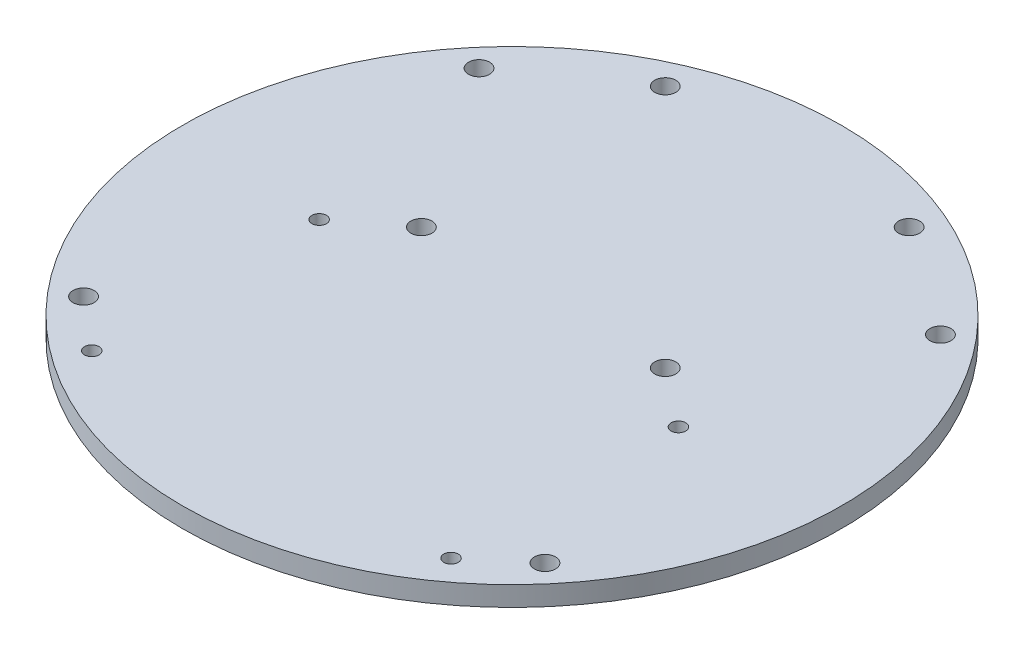
SolidWorks part; units mm, degrees
ref_plane "Front Plane" through (0, 0, 0) normal (0, 0, 1) x (1, 0, 0)
ref_plane "Top Plane" through (0, 0, 0) normal (0, 1, 0) x (1, 0, 0)
ref_plane "Right Plane" through (0, 0, 0) normal (1, 0, 0) x (0, 0, -1)
sketch "Sketch1" plane through (0, 0, 0) normal (0, 1, 0) x (1, 0, 0)
  line L0 (0, 50) -> (0, -50) construction
  line L1 (-27.25, -2) -> (27.25, -2) construction
  line L2 (-27.25, -2) -> (-27.25, -36.5) construction
  line L3 (-27.25, -36.5) -> (27.25, -36.5) construction
  line L4 (27.25, -2) -> (27.25, -36.5) construction
  line L5 (-27.25, -2) -> (27.25, -36.5) construction
  line L6 (-27.25, -36.5) -> (27.25, -2) construction
  line L7 (-50, 0) -> (50, 0) construction
  line L8 (-27.25, -19.25) -> (27.25, -19.25) construction
  line L9 (-18.5, 23.25) -> (18.5, 23.25) construction
  line L10 (-18.5, 4.75) -> (18.5, 4.75) construction
  line L11 (-18.5, 4.75) -> (-18.5, 41.75) construction
  line L12 (-18.5, 41.75) -> (18.5, 41.75) construction
  line L13 (18.5, 4.75) -> (18.5, 41.75) construction
  line L14 (-18.5, 4.75) -> (18.5, 41.75) construction
  line L15 (-18.5, 41.75) -> (18.5, 4.75) construction
  line L17 (-35, -30) -> (35, -30) construction
  line L18 (-35, -30) -> (-35, 30) construction
  line L19 (-35, 30) -> (35, 30) construction
  line L20 (35, -30) -> (35, 30) construction
  line L21 (-35, -30) -> (35, 30) construction
  line L22 (-35, 30) -> (35, -30) construction
  line L23 (-30, -39.25) -> (30, -39.25) construction
  line L24 (-30, -39.25) -> (-30, 0.75) construction
  line L25 (-30, 0.75) -> (30, 0.75) construction
  line L26 (30, -39.25) -> (30, 0.75) construction
  line L27 (-30, -39.25) -> (30, 0.75) construction
  line L28 (-30, 0.75) -> (30, -39.25) construction
  line L29 (-21.5, 44.75) -> (21.5, 44.75) construction
  line L30 (-21.5, 44.75) -> (-21.5, 1.75) construction
  line L31 (-21.5, 1.75) -> (21.5, 1.75) construction
  line L32 (21.5, 44.75) -> (21.5, 1.75) construction
  line L33 (-21.5, 44.75) -> (21.5, 1.75) construction
  line L34 (-21.5, 1.75) -> (21.5, 44.75) construction
  circle A0 centre (0, 0) radius 50
  circle A1 centre (-27.25, -2) radius 1.1
  circle A2 centre (-27.25, -36.5) radius 1.1
  circle A3 centre (27.25, -2) radius 1.1
  circle A4 centre (27.25, -36.5) radius 1.1
  circle A5 centre (-18.5, 41.75) radius 1.6
  circle A6 centre (18.5, 41.75) radius 1.6
  circle A7 centre (18.5, 4.75) radius 1.6
  circle A8 centre (-18.5, 4.75) radius 1.6
  circle A9 centre (-35, -30) radius 1.6
  circle A10 centre (-35, 30) radius 1.6
  circle A11 centre (35, -30) radius 1.6
  circle A12 centre (35, 30) radius 1.6
  point P3 (0, -19.25)
  point P18 (0, 23.25)
  point P37 (0, -19.25)
  point P42 (0, 23.25)
  dimension "D1" = 100
  dimension "D5" = 2.2
  dimension "D9" = 3.2
  dimension "D12" = 3.2
  dimension "D2" = 34.5
  dimension "D3" = 54.5
  dimension "D4" = 2
  dimension "D6" = 37
  dimension "D7" = 37
  dimension "D8" = 4.75
  dimension "D10" = 70
  dimension "D11" = 60
  dimension "D13" = 40
  dimension "D14" = 60
  dimension "D15" = 43
  dimension "D16" = 43
extrude "Boss-Extrude1" add sketch "Sketch1" along normal blind 3
